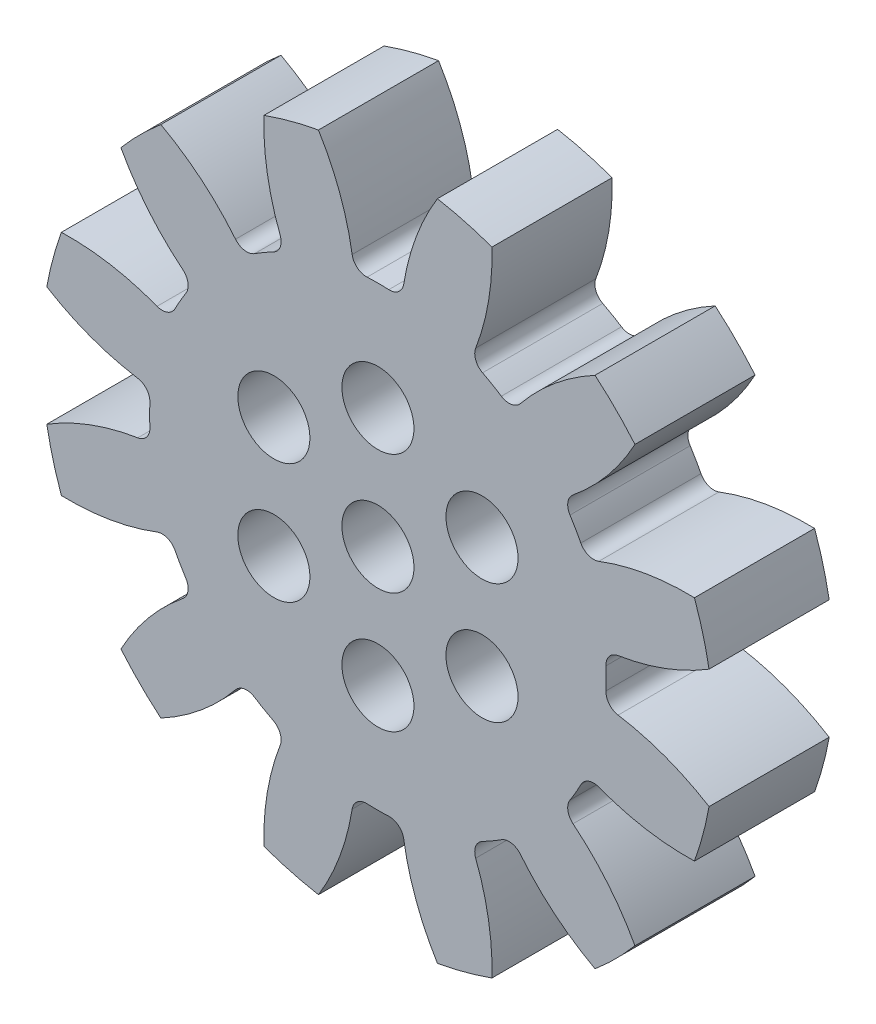
SolidWorks part; units mm, degrees
ref_plane "Front Plane" through (0, 0, 0) normal (0, 0, 1) x (1, 0, 0)
ref_plane "Top Plane" through (0, 0, 0) normal (0, 1, 0) x (1, 0, 0)
ref_plane "Right Plane" through (0, 0, 0) normal (1, 0, 0) x (0, 0, -1)
sketch "Sketch1" plane through (0, 0, 0) normal (0, 0, 1) x (1, 0, 0)
  circle A0 centre (0, 0) radius 12
  circle A1 centre (0, 0) radius 9.5
  circle A2 centre (0, 0) radius 14
  dimension "D1" = 24
  dimension "D2" = 28
  dimension "D3" = 4.5
extrude "Boss-Extrude1" add sketch "Sketch1" along normal mid plane 5 contours A2
sketch "Sketch2" plane through (0, 0, 0) normal (0, 0, 1) x (1, 0, 0)
  line L0 (0, 0) -> (0, 14) construction
  line L1 (-0.9997, 9.4472) -> (0, 0) construction
  line L2 (-1.5663, 11.8973) -> (1.5663, 11.8973) construction
  line L3 (0, 7.5939) -> (-2.7213, 15.0705) construction
  line L4 (0, 0) -> (3.6235, 13.523) construction
  line L5 (1.5663, 11.8973) -> (4.5922, 11.0866) construction
  circle A0 centre (0, 0) radius 14 construction
  arc A1 (-3.3146, 14.9512) -> (-0.9997, 9.4472) centre (-11.2897, 8.3583) cw
  arc A2 (3.3146, 14.9512) -> (0.9997, 9.4472) centre (11.2897, 8.3583) ccw
  arc A3 (3.3146, 14.9512) -> (-3.3146, 14.9512) centre (0, 0) ccw
  arc A4 (0.9997, 9.4472) -> (-0.9997, 9.4472) centre (0, 0) ccw
  circle A6 centre (0, 0) radius 9.5 construction
  circle A7 centre (0, 0) radius 12 construction
  dimension "D1" = 20
  dimension "D2" = 15
extrude "Cut-Extrude1" cut sketch "Sketch2" against normal through all both and the other way through all
fillet "Fillet1" radius 0.6 1 edges at (-0.9997, 9.4472, 0)
fillet "Fillet2" radius 0.6 1 edges at (0.9997, 9.4472, 0)
sketch "Sketch3" plane through (0, 0, 2.5) normal (0, 0, 1) x (1, 0, 0)
pattern_circular "CirPattern2" count 12 over 360 about axis through (0, 0, 0) along (0, 0, 1) of "Fillet1", "Cut-Extrude1", "Fillet2"
sketch "Sketch4" plane through (0, 0, 2.5) normal (0, 0, 1) x (1, 0, 0)
  line L0 (0, 0) -> (0, 8.1574) construction
  circle A0 centre (0, 0) radius 1.5
  circle A1 centre (0, 5) radius 1.5
  circle A2 centre (4.3301, 2.5) radius 1.5
  circle A3 centre (4.3301, -2.5) radius 1.5
  circle A4 centre (0, -5) radius 1.5
  circle A5 centre (-4.3301, -2.5) radius 1.5
  circle A6 centre (-4.3301, 2.5) radius 1.5
  point P18 (0, 0)
  dimension "D1" = 3
  dimension "D2" = 3
  dimension "D3" = 5
  dimension "D4" = 6
extrude "Cut-Extrude2" cut sketch "Sketch4" against normal through all both and the other way through all
sketch "Sketch5" [suppressed] plane through (0, 0, 2.5) normal (0, 0, 1) x (1, 0, 0)
  circle A0 centre (0, 5) radius 1.6
  circle A1 centre (-4.3301, -2.5) radius 1.5
  circle A2 centre (-4.3301, -2.5) radius 1.5 construction
  circle A3 centre (0, -5) radius 1.5
  circle A4 centre (0, -5) radius 1.5 construction
  circle A5 centre (4.3301, -2.5) radius 1.5
  circle A6 centre (4.3301, -2.5) radius 1.5 construction
  circle A7 centre (4.3301, 2.5) radius 1.5
  circle A8 centre (4.3301, 2.5) radius 1.5 construction
  circle A9 centre (0, 5) radius 1.5
  circle A10 centre (0, 5) radius 1.5 construction
  circle A11 centre (0, 0) radius 1.5
  circle A12 centre (0, 0) radius 1.5 construction
  circle A13 centre (-4.3301, 2.5) radius 1.5
  circle A14 centre (-4.3301, 2.5) radius 1.5 construction
  circle A15 centre (4.3301, 2.5) radius 1.6
  circle A16 centre (4.3301, -2.5) radius 1.6
  circle A17 centre (0, -5) radius 1.6
  circle A18 centre (0, 0) radius 1.6
  circle A19 centre (-4.3301, -2.5) radius 1.6
  circle A20 centre (-4.3301, 2.5) radius 1.6
  dimension "D8" = 3.2
  dimension "D1" = 0
  dimension "D2" = 0
  dimension "D3" = 0
  dimension "D4" = 0
  dimension "D5" = 0
  dimension "D6" = 0
  dimension "D7" = 0
extrude "Cut-Extrude3" [suppressed] cut sketch "Sketch5" against normal through all
equation "\"Number of Teeth\"= 12"
equation "\"Module\"= 2mm"
equation "\"D2@Sketch2\"=180 / \"Number of Teeth\""
equation "\"D1@Sketch1\"= \"Module\" * \"Number of Teeth\""
equation "\"D2@Sketch1\"=(\"Number of Teeth\" + 2) * \"Module\""
equation "\"D3@Sketch1\"= \"Module\" * 2.25"
equation "\"D1@CirPattern2\"= \"Number of Teeth\""
